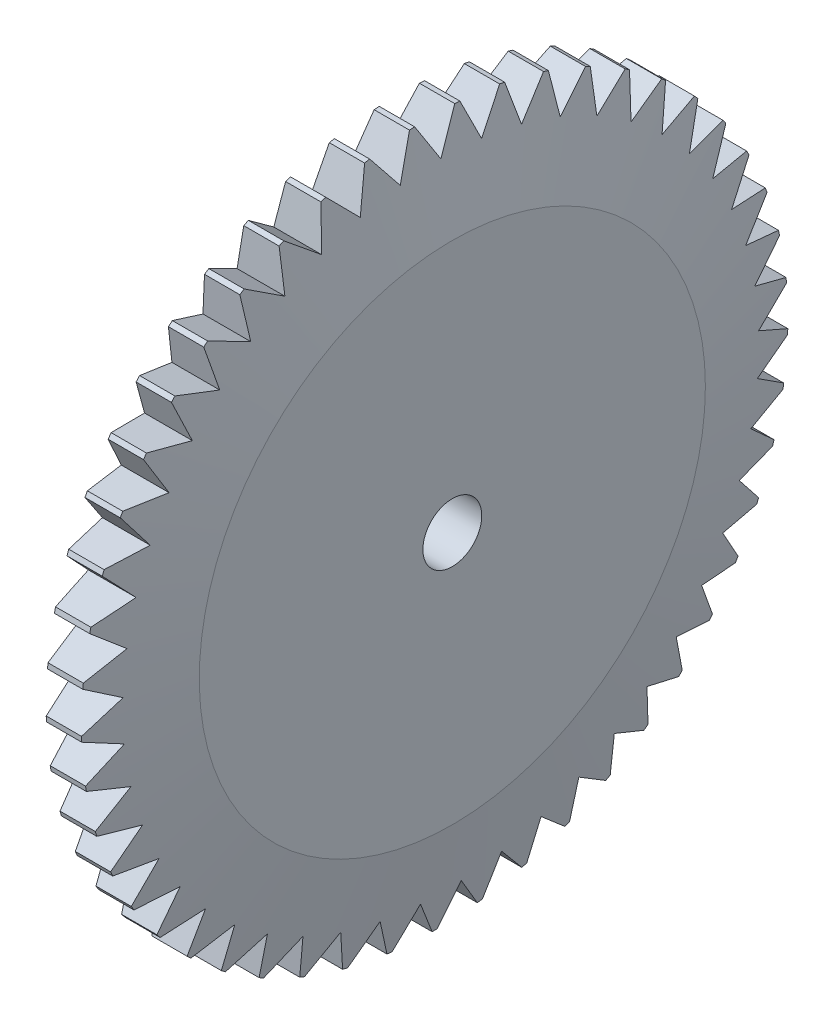
SolidWorks part; units mm, degrees
ref_plane "Front Plane" through (0, 0, 0) normal (0, 0, 1) x (1, 0, 0)
ref_plane "Top Plane" through (0, 0, 0) normal (0, 1, 0) x (1, 0, 0)
ref_plane "Right Plane" through (0, 0, 0) normal (1, 0, 0) x (0, 0, -1)
sketch "Sketch1" plane through (0, 0, 0) normal (1, 0, 0) x (0, 0, -1)
  circle A0 centre (0, 0) radius 60
  circle A1 centre (0, 0) radius 5
  dimension "D1" = 120
  dimension "D2" = 10
extrude "Boss-Extrude1" add sketch "Sketch1" along normal mid plane 12
sketch "Sketch2" plane through (6, 0, 0) normal (1, 0, 0) x (0, 0, -1)
  line L0 (0, 1.033) -> (0, 49.8392) construction
  line L1 (0, 60) -> (0, 54)
  line L2 (0, 54) -> (3.4082, 59.9031)
  line L4 (-3.4082, 59.9031) -> (0, 54)
  circle A0 centre (0, 0) radius 60 construction
  arc A1 (-3.4082, 59.9031) -> (3.4082, 59.9031) centre (0, 54) cw
  dimension "D1" = 30
  dimension "D2" = 30
  dimension "D3" = 6
chamfer "Chamfer2" distance 3 angle 80 1 edges at (6, 0, -60)
chamfer "Chamfer3" distance 3 angle 80 1 edges at (-6, 0, -60)
extrude "Cut-Extrude2" cut sketch "Sketch2" against normal blind 12 contours L2 A1 L4
pattern_circular "CirPattern2" count 49 over 360 about axis through (0, 0, 0) along (1, 0, 0) of "Cut-Extrude2"
